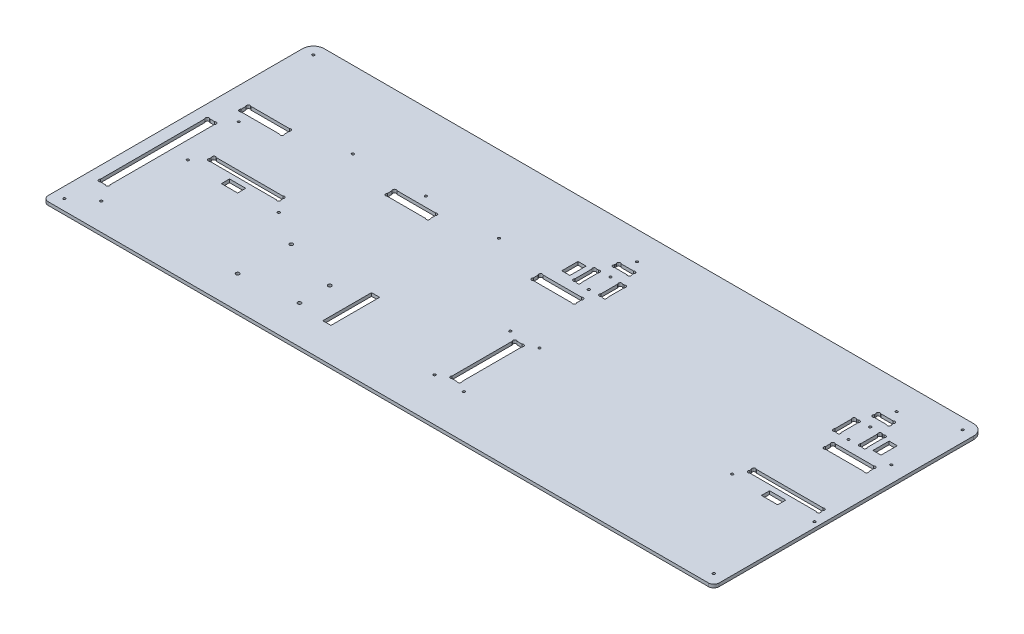
SolidWorks part; units mm, degrees
ref_plane "Plan de face" through (0, 0, 0) normal (0, 0, 1) x (1, 0, 0)
ref_plane "Plan de dessus" through (0, 0, 0) normal (0, 1, 0) x (1, 0, 0)
ref_plane "Plan de droite" through (0, 0, 0) normal (1, 0, 0) x (0, 0, -1)
sketch "Esquisse1" plane through (0, 0, 0) normal (0, 1, 0) x (1, 0, 0)
  line L26 (317, 211.2627) -> (317, 212.7373)
  line L28 (319.2627, 215) -> (330.7373, 215)
  line L29 (333, 211.2627) -> (333, 212.7373)
  line L30 (330.7373, 209) -> (319.2627, 209)
  line L31 (312.2627, 179.5) -> (313.7373, 179.5)
  line L32 (312.2627, 199.5) -> (313.7373, 199.5)
  line L33 (310, 197.2373) -> (310, 181.7627)
  line L34 (316, 181.7627) -> (316, 197.2373)
  line L35 (334, 181.7627) -> (334, 197.2373)
  line L36 (340, 197.2373) -> (340, 181.7627)
  line L37 (337.7373, 199.5) -> (336.2627, 199.5)
  line L38 (337.7373, 179.5) -> (336.2627, 179.5)
  line L39 (552.2627, 179.5) -> (553.7373, 179.5)
  line L40 (552.2627, 199.5) -> (553.7373, 199.5)
  line L41 (550, 197.2373) -> (550, 181.7627)
  line L42 (556, 181.7627) -> (556, 197.2373)
  line L43 (574, 181.7627) -> (574, 197.2373)
  line L44 (580, 197.2373) -> (580, 181.7627)
  line L45 (577.7373, 199.5) -> (576.2627, 199.5)
  line L46 (577.7373, 179.5) -> (576.2627, 179.5)
  line L47 (559.2627, 209) -> (570.7373, 209)
  line L48 (557, 211.2627) -> (557, 212.7373)
  line L49 (570.7373, 215) -> (559.2627, 215)
  line L50 (573, 211.2627) -> (573, 212.7373)
  line L55 (560, 167.7373) -> (560, 163.2627)
  line L56 (600, 167.7373) -> (600, 163.2627)
  line L57 (562.2627, 170) -> (597.7373, 170)
  line L58 (597.7373, 161) -> (562.2627, 161)
  line L59 (292.2627, 161) -> (327.7373, 161)
  line L60 (327.7373, 170) -> (292.2627, 170)
  line L61 (290, 167.7373) -> (290, 163.2627)
  line L62 (330, 167.7373) -> (330, 163.2627)
  line L64 (20, 167.7373) -> (20, 163.2627)
  line L65 (60, 167.7373) -> (60, 163.2627)
  line L66 (22.2627, 170) -> (57.7373, 170)
  line L67 (57.7373, 161) -> (22.2627, 161)
  line L70 (155, 167.7373) -> (155, 163.2627)
  line L71 (195, 167.7373) -> (195, 163.2627)
  line L72 (157.2627, 170) -> (192.7373, 170)
  line L73 (192.7373, 161) -> (157.2627, 161)
  line L76 (10, 250) -> (610, 250)
  line L77 (0, 240) -> (0, 0)
  line L78 (0, 0) -> (620, 0)
  line L79 (620, 240) -> (620, 0)
  line L84 (13.2627, 40) -> (17.7373, 40)
  line L85 (13.2627, 141) -> (17.7373, 141)
  line L86 (11, 138.7373) -> (11, 42.2627)
  line L87 (20, 42.2627) -> (20, 138.7373)
  line L98 (337.7373, 45) -> (333.2627, 45)
  line L99 (337.7373, 105) -> (333.2627, 105)
  line L100 (340, 47.2627) -> (340, 102.7373)
  line L101 (331, 102.7373) -> (331, 47.2627)
  line L109 (610, 109.2627) -> (610, 110.7373)
  line L110 (544, 109.2627) -> (544, 110.7373)
  line L111 (607.7373, 107) -> (546.2627, 107)
  line L112 (546.2627, 113) -> (607.7373, 113)
  line L113 (108.7373, 113) -> (47.2627, 113)
  line L114 (47.2627, 107) -> (108.7373, 107)
  line L115 (111, 109.2627) -> (111, 110.7373)
  line L116 (45, 109.2627) -> (45, 110.7373)
  arc A0 (319.2627, 215) -> (317, 212.7373) centre (318.1314, 213.8686) ccw
  arc A1 (319.2627, 209) -> (317, 211.2627) centre (318.1314, 210.1314) cw
  arc A2 (330.7373, 209) -> (333, 211.2627) centre (331.8686, 210.1314) ccw
  arc A3 (330.7373, 215) -> (333, 212.7373) centre (331.8686, 213.8686) cw
  arc A4 (313.7373, 179.5) -> (316, 181.7627) centre (314.8686, 180.6314) ccw
  arc A5 (312.2627, 179.5) -> (310, 181.7627) centre (311.1314, 180.6314) cw
  arc A6 (312.2627, 199.5) -> (310, 197.2373) centre (311.1314, 198.3686) ccw
  arc A7 (313.7373, 199.5) -> (316, 197.2373) centre (314.8686, 198.3686) cw
  arc A8 (336.2627, 179.5) -> (334, 181.7627) centre (335.1314, 180.6314) cw
  arc A9 (336.2627, 199.5) -> (334, 197.2373) centre (335.1314, 198.3686) ccw
  arc A10 (337.7373, 199.5) -> (340, 197.2373) centre (338.8686, 198.3686) cw
  arc A11 (337.7373, 179.5) -> (340, 181.7627) centre (338.8686, 180.6314) ccw
  arc A12 (552.2627, 179.5) -> (550, 181.7627) centre (551.1314, 180.6314) cw
  arc A13 (552.2627, 199.5) -> (550, 197.2373) centre (551.1314, 198.3686) ccw
  arc A14 (553.7373, 199.5) -> (556, 197.2373) centre (554.8686, 198.3686) cw
  arc A15 (553.7373, 179.5) -> (556, 181.7627) centre (554.8686, 180.6314) ccw
  arc A16 (576.2627, 199.5) -> (574, 197.2373) centre (575.1314, 198.3686) ccw
  arc A17 (577.7373, 199.5) -> (580, 197.2373) centre (578.8686, 198.3686) cw
  arc A18 (577.7373, 179.5) -> (580, 181.7627) centre (578.8686, 180.6314) ccw
  arc A19 (576.2627, 179.5) -> (574, 181.7627) centre (575.1314, 180.6314) cw
  arc A20 (559.2627, 215) -> (557, 212.7373) centre (558.1314, 213.8686) ccw
  arc A21 (559.2627, 209) -> (557, 211.2627) centre (558.1314, 210.1314) cw
  arc A22 (570.7373, 209) -> (573, 211.2627) centre (571.8686, 210.1314) ccw
  arc A23 (570.7373, 215) -> (573, 212.7373) centre (571.8686, 213.8686) cw
  arc A29 (560, 163.2627) -> (562.2627, 161) centre (561.1314, 162.1314) ccw
  arc A30 (560, 167.7373) -> (562.2627, 170) centre (561.1314, 168.8686) cw
  arc A31 (600, 167.7373) -> (597.7373, 170) centre (598.8686, 168.8686) ccw
  arc A32 (600, 163.2627) -> (597.7373, 161) centre (598.8686, 162.1314) cw
  arc A34 (290, 163.2627) -> (292.2627, 161) centre (291.1314, 162.1314) ccw
  arc A35 (290, 167.7373) -> (292.2627, 170) centre (291.1314, 168.8686) cw
  arc A36 (330, 167.7373) -> (327.7373, 170) centre (328.8686, 168.8686) ccw
  arc A37 (330, 163.2627) -> (327.7373, 161) centre (328.8686, 162.1314) cw
  arc A40 (20, 163.2627) -> (22.2627, 161) centre (21.1314, 162.1314) ccw
  arc A41 (20, 167.7373) -> (22.2627, 170) centre (21.1314, 168.8686) cw
  arc A42 (60, 167.7373) -> (57.7373, 170) centre (58.8686, 168.8686) ccw
  arc A43 (60, 163.2627) -> (57.7373, 161) centre (58.8686, 162.1314) cw
  arc A44 (155, 163.2627) -> (157.2627, 161) centre (156.1314, 162.1314) ccw
  arc A45 (155, 167.7373) -> (157.2627, 170) centre (156.1314, 168.8686) cw
  arc A46 (195, 163.2627) -> (192.7373, 161) centre (193.8686, 162.1314) cw
  arc A47 (195, 167.7373) -> (192.7373, 170) centre (193.8686, 168.8686) ccw
  arc A50 (17.7373, 40) -> (20, 42.2627) centre (18.8686, 41.1314) ccw
  arc A52 (13.2627, 40) -> (11, 42.2627) centre (12.1314, 41.1314) cw
  arc A53 (17.7373, 141) -> (20, 138.7373) centre (18.8686, 139.8686) cw
  arc A54 (13.2627, 141) -> (11, 138.7373) centre (12.1314, 139.8686) ccw
  arc A56 (10, 250) -> (0, 240) centre (10, 240) ccw
  arc A57 (610, 250) -> (620, 240) centre (610, 240) cw
  arc A59 (331, 47.2627) -> (333.2627, 45) centre (332.1314, 46.1314) ccw
  arc A60 (340, 47.2627) -> (337.7373, 45) centre (338.8686, 46.1314) cw
  arc A61 (331, 102.7373) -> (333.2627, 105) centre (332.1314, 103.8686) cw
  arc A62 (340, 102.7373) -> (337.7373, 105) centre (338.8686, 103.8686) ccw
  arc A64 (607.7373, 107) -> (610, 109.2627) centre (608.8686, 108.1314) ccw
  circle A65 centre (539, 98) radius 1.1
  arc A66 (607.7373, 113) -> (610, 110.7373) centre (608.8686, 111.8686) cw
  circle A67 centre (615, 98) radius 1.1
  arc A68 (546.2627, 113) -> (544, 110.7373) centre (545.1314, 111.8686) ccw
  arc A69 (546.2627, 107) -> (544, 109.2627) centre (545.1314, 108.1314) cw
  arc A70 (108.7373, 107) -> (111, 109.2627) centre (109.8686, 108.1314) ccw
  arc A71 (108.7373, 113) -> (111, 110.7373) centre (109.8686, 111.8686) cw
  arc A73 (47.2627, 113) -> (45, 110.7373) centre (46.1314, 111.8686) ccw
  arc A75 (47.2627, 107) -> (45, 109.2627) centre (46.1314, 108.1314) cw
  point P1 (337, 199.5)
  point P7 (340, 189.5)
  dimension "D25" = 6
  dimension "D28" = 16
  dimension "D29" = 20
  dimension "D32" = 9.5
  dimension "D33" = 35
  dimension "D39" = 10
  dimension "D49" = 1.1314
  dimension "D57" = 6
  dimension "D55" = 10
  dimension "D62" = 5
  dimension "D63" = 1.6
  dimension "D64" = 9
  dimension "D65" = 1.1314
  dimension "D66" = 1.1314
  dimension "D67" = 620
  dimension "D9" = 2.2627
  dimension "D10" = 1.6
  dimension "D78" = 3.7373
  dimension "D14" = 1.6
  dimension "D36" = 1.6
  dimension "D61" = 1.6
  dimension "D95" = 1.6
  dimension "D107" = 1.6
  dimension "D118" = 1.6
  dimension "D119" = 1.6
  dimension "D128" = 6
  dimension "D141" = 1.6
  dimension "D58" = 2.2
  dimension "D2" = 250
  dimension "D8" = 20
  dimension "D13" = 40
  dimension "D16" = 1.1314
  dimension "D17" = 1.1314
  dimension "D19" = 2.2627
  dimension "D20" = 2.2627
  dimension "D21" = 80
  dimension "D22" = 9
  dimension "D23" = 1.1314
  dimension "D24" = 1.1314
  dimension "D26" = 6
  dimension "D27" = 6
  dimension "D30" = 40
  dimension "D31" = 18
  dimension "D37" = 1.1314
  dimension "D38" = 2.2627
  dimension "D40" = 1.1314
  dimension "D41" = 1.1314
  dimension "D42" = 1.1314
  dimension "D43" = 1.1314
  dimension "D45" = 1
  dimension "D46" = 1.1314
  dimension "D47" = 1.1314
  dimension "D48" = 1.1314
  dimension "D51" = 3.7373
  dimension "D52" = 66
  dimension "D53" = 10
  dimension "D54" = 66
  dimension "D56" = 107
  dimension "D59" = 1.1314
  dimension "D60" = 2.2627
  dimension "D68" = 60
  dimension "D70" = 6
  dimension "D72" = 1.1314
  dimension "D73" = 1.1314
  dimension "D74" = 63.7373
  dimension "D75" = 2.2627
  dimension "D76" = 2.2627
  dimension "D77" = 45
  dimension "D79" = 45
  dimension "D83" = 280
  dimension "D84" = 1.1314
  dimension "D85" = 1.1314
  dimension "D86" = 1.1314
  dimension "D87" = 1.1314
  dimension "D88" = 9
  dimension "D89" = 101
  dimension "D90" = 40
  dimension "D91" = 11
  dimension "D96" = 1.1314
  dimension "D97" = 1.1314
  dimension "D98" = 1.1314
  dimension "D100" = 1.1314
  dimension "D105" = 9
  dimension "D106" = 40
  dimension "D108" = 20
  dimension "D109" = 80
  dimension "D110" = 1.1314
  dimension "D111" = 1.1314
  dimension "D112" = 1.1314
  dimension "D113" = 1.1314
  dimension "D114" = 40
  dimension "D115" = 95
  dimension "D116" = 95
  dimension "D117" = 40
  dimension "D120" = 1.1314
  dimension "D121" = 1.1314
  dimension "D122" = 1.1314
  dimension "D123" = 1.1314
  dimension "D124" = 1.1314
  dimension "D125" = 1.1314
  dimension "D126" = 1.1314
  dimension "D127" = 1.1314
  dimension "D129" = 6
  dimension "D130" = 6
  dimension "D132" = 20
  dimension "D133" = 16
  dimension "D135" = 35
  dimension "D136" = 9.5
  dimension "D139" = 1
  dimension "D140" = 18
  dimension "D142" = 1.1314
  dimension "D143" = 1.1314
  dimension "D144" = 1.1314
  dimension "D145" = 1.1314
  dimension "D146" = 1.1314
  dimension "D147" = 1.1314
  dimension "D148" = 1.1314
  dimension "D149" = 1.1314
  dimension "D150" = 1.1314
  dimension "D151" = 1.1314
  dimension "D152" = 1.1314
  dimension "D153" = 1.1314
  dimension "D154" = 9
  dimension "D155" = 5
extrude "Extrusion1" add sketch "Esquisse1" along normal blind 3
sketch "Esquisse2" plane through (0, 3, 0) normal (0, 1, 0) x (-1, 0, 0)
  line L0 (-610, -250) -> (-10, -250) construction
  line L5 (-620, 21.4973) -> (-620, -261.3021) construction
  line L7 (-573, -142.8) -> (-72, -142.8)
  line L8 (-573, -142.8) -> (-573, -147)
  line L9 (-573, -147) -> (-72, -147)
  line L10 (-72, -142.8) -> (-72, -147)
  dimension "D1" = 47
  dimension "D2" = 4.2
  dimension "D3" = 501
  dimension "D4" = 103
extrude "Enlèv. mat.-Extru.1" [suppressed] cut sketch "Esquisse2" against normal through all
sketch "Esquisse3" plane through (0, 3, 0) normal (0, 1, 0) x (1, 0, 0)
  line L0 (574, 197.2373) -> (574, 181.7627) construction
  line L1 (556, 181.7627) -> (556, 197.2373) construction
  line L2 (559.2627, 209) -> (570.7373, 209) construction
  line L4 (576.2627, 179.5) -> (577.7373, 179.5) construction
  line L5 (577.7373, 199.5) -> (576.2627, 199.5) construction
  line L6 (334, 197.2373) -> (334, 181.7627) construction
  circle A0 centre (565, 179.5) radius 1.1
  circle A1 centre (565, 199.5) radius 1.1
  circle A2 centre (325, 179.5) radius 1.1
  circle A3 centre (325, 199.5) radius 1.1
  dimension "D1" = 2.2
  dimension "D2" = 9
  dimension "D3" = 9
  dimension "D4" = 20
  dimension "D5" = 9.5
  dimension "D6" = 0
  dimension "D7" = 0
  dimension "D8" = 9
extrude "Enlèv. mat.-Extru.2" cut sketch "Esquisse3" against normal through all
fillet "Congé1" radius 5 2 edges at (620, 1.5, 0) (0, 1.5, 0)
sketch "Esquisse4" plane through (0, 0, 0) normal (0, -1, 0) x (1, 0, 0)
  line L0 (0, -240) -> (0, -5) construction
  line L1 (5, 0) -> (615, 0) construction
  line L2 (610, -250) -> (10, -250) construction
  line L3 (620, -5) -> (620, -240) construction
  circle A0 centre (10, -10) radius 1.1
  circle A1 centre (610, -10) radius 1.1
  circle A2 centre (610, -240) radius 1.1
  circle A3 centre (10, -240) radius 1.1
  dimension "D1" = 2.2
  dimension "D2" = 10
  dimension "D3" = 10
  dimension "D4" = 10
  dimension "D5" = 10
  dimension "D6" = 10
  dimension "D7" = 10
  dimension "D8" = 10
  dimension "D9" = 10
extrude "Enlèv. mat.-Extru.3" cut sketch "Esquisse4" against normal through all
sketch "Esquisse5" plane through (0, 3, 0) normal (0, 1, 0) x (1, 0, 0)
  line L1 (0, 240) -> (0, 5) construction
  line L2 (5, 0) -> (615, 0) construction
  circle A0 centre (151.27, 78.26) radius 1.59
  circle A1 centre (150, 30) radius 1.59
  circle A2 centre (202.07, 63.02) radius 1.59
  circle A3 centre (202.07, 35.08) radius 1.59
  dimension "D1" = 3.18
  dimension "D7" = 30
  dimension "D2" = 48.26
  dimension "D3" = 27.94
  dimension "D4" = 52.07
  dimension "D5" = 5.08
  dimension "D6" = 150
  dimension "D8" = 1.27
extrude "Enlèv. mat.-Extru.4" cut sketch "Esquisse5" against normal through all
sketch "Esquisse6" plane through (0, 3, 0) normal (0, 1, 0) x (1, 0, 0)
  line L0 (544, 110.7373) -> (544, 109.2627) construction
  line L1 (569.5, 102) -> (584.5, 102)
  line L2 (569.5, 102) -> (569.5, 94.5)
  line L3 (569.5, 94.5) -> (584.5, 94.5)
  line L4 (584.5, 102) -> (584.5, 94.5)
  line L5 (610, 109.2627) -> (610, 110.7373) construction
  line L6 (546.2627, 107) -> (607.7373, 107) construction
  line L8 (585, 197) -> (592.5, 197)
  line L9 (585, 197) -> (585, 182)
  line L10 (585, 182) -> (592.5, 182)
  line L11 (592.5, 197) -> (592.5, 182)
  line L12 (305, 197) -> (297.5, 197)
  line L13 (305, 197) -> (305, 182)
  line L14 (305, 182) -> (297.5, 182)
  line L15 (297.5, 197) -> (297.5, 182)
  line L16 (577.7373, 199.5) -> (576.2627, 199.5) construction
  line L17 (576.2627, 179.5) -> (577.7373, 179.5) construction
  line L18 (580, 181.7627) -> (580, 197.2373) construction
  line L19 (310, 197.2373) -> (310, 181.7627) construction
  line L20 (313.7373, 199.5) -> (312.2627, 199.5) construction
  line L21 (45, 110.7373) -> (45, 109.2627) construction
  line L22 (227.07, 76.63) -> (234.57, 76.63)
  line L23 (227.07, 76.63) -> (227.07, 31.63)
  line L24 (227.07, 31.63) -> (234.57, 31.63)
  line L25 (234.57, 76.63) -> (234.57, 31.63)
  line L26 (70.5, 102) -> (85.5, 102)
  line L27 (70.5, 102) -> (70.5, 94.5)
  line L28 (70.5, 94.5) -> (85.5, 94.5)
  line L29 (85.5, 102) -> (85.5, 94.5)
  circle A0 centre (150, 30) radius 1.59 construction
  circle A1 centre (151.27, 78.26) radius 1.59 construction
  circle A2 centre (202.07, 63.02) radius 1.59 construction
  dimension "D1" = 15
  dimension "D2" = 7.5
  dimension "D3" = 25.5
  dimension "D4" = 25.5
  dimension "D5" = 5
  dimension "D6" = 7.5
  dimension "D7" = 15
  dimension "D8" = 15
  dimension "D9" = 7.5
  dimension "D10" = 2.5
  dimension "D11" = 2.5
  dimension "D12" = 5
  dimension "D13" = 5
  dimension "D14" = 2.5
  dimension "D15" = 7.5
  dimension "D16" = 45
  dimension "D17" = 1.63
  dimension "D18" = 1.63
  dimension "D19" = 25
  dimension "D20" = 15
  dimension "D21" = 25.5
extrude "Enlèv. mat.-Extru.5" cut sketch "Esquisse6" against normal through all
sketch "Esquisse7" plane through (0, 3, 0) normal (0, 1, 0) x (1, 0, 0)
  line L1 (5, 0) -> (615, 0) construction
  line L2 (331, 102.7373) -> (331, 47.2627) construction
  line L3 (340, 47.2627) -> (340, 102.7373) construction
  line L4 (570.7373, 215) -> (559.2627, 215) construction
  line L5 (330.7373, 215) -> (319.2627, 215) construction
  line L6 (597.7373, 170) -> (562.2627, 170) construction
  line L7 (192.7373, 170) -> (157.2627, 170) construction
  line L8 (0, 240) -> (0, 5) construction
  line L10 (47.2627, 107) -> (108.7373, 107) construction
  line L11 (45, 110.7373) -> (45, 109.2627) construction
  line L12 (111, 109.2627) -> (111, 110.7373) construction
  circle A0 centre (349, 110) radius 1.1
  circle A1 centre (349, 40) radius 1.1
  circle A2 centre (322, 110) radius 1.1
  circle A3 centre (322, 40) radius 1.1
  circle A4 centre (605, 179) radius 1.1
  circle A5 centre (565, 224) radius 1.1
  circle A6 centre (325, 224) radius 1.1
  circle A7 centre (175, 179) radius 1.1
  circle A8 centre (242.5, 179) radius 1.1
  circle A9 centre (107.5, 179) radius 1.1
  circle A10 centre (120, 98) radius 1.1
  circle A11 centre (36, 98) radius 1.1
  circle A12 centre (29, 152) radius 1.1
  circle A13 centre (29, 25) radius 1.1
  point P34 (325, 215)
  point P38 (565, 215)
  point P47 (175, 170)
  dimension "D1" = 2.2
  dimension "D2" = 40
  dimension "D3" = 9
  dimension "D4" = 9
  dimension "D5" = 70
  dimension "D6" = 9
  dimension "D7" = 40
  dimension "D8" = 9
  dimension "D9" = 9
  dimension "D10" = 67.5
  dimension "D11" = 67.5
  dimension "D12" = 127
  dimension "D13" = 25
  dimension "D14" = 29
  dimension "D15" = 9
  dimension "D16" = 9
  dimension "D17" = 9
extrude "Enlèv. mat.-Extru.6" cut sketch "Esquisse7" against normal through all
